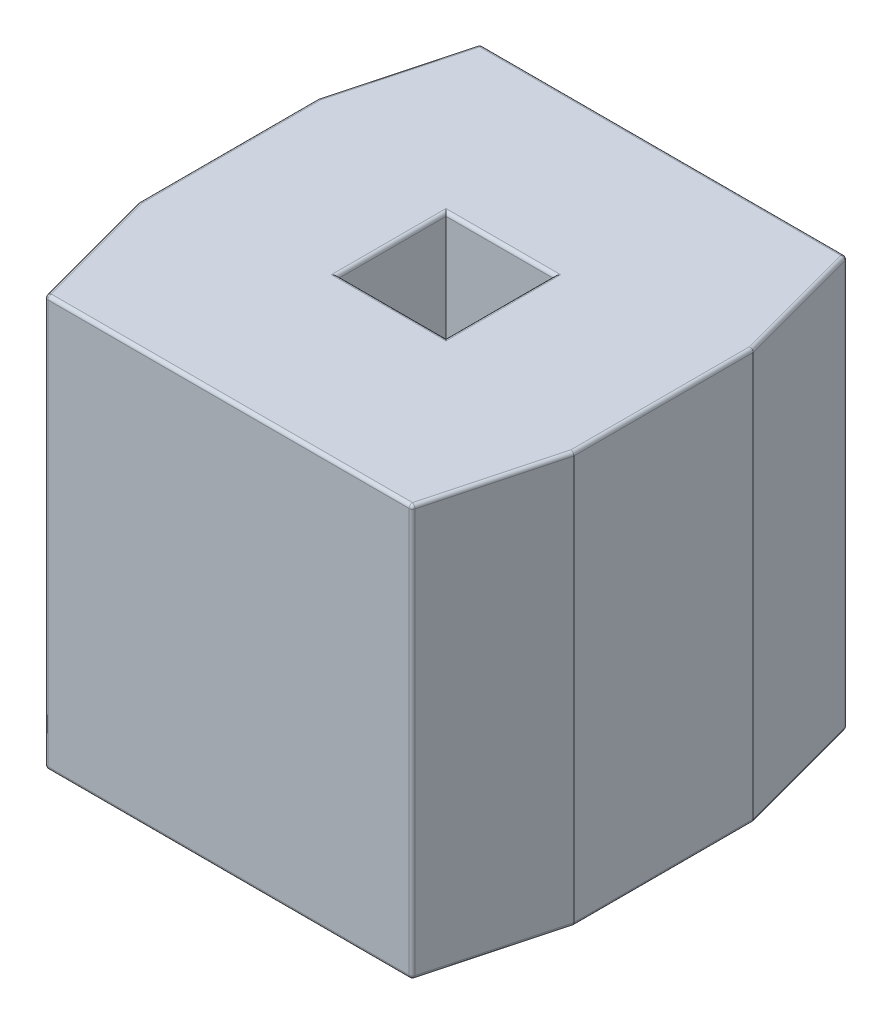
SolidWorks part; units mm, degrees
material "PVC 0.007 Plasticized"
ref_plane "Front Plane" through (0, 0, 0) normal (0, 0, 1) x (1, 0, 0)
ref_plane "Top Plane" through (0, 0, 0) normal (0, 1, 0) x (1, 0, 0)
ref_plane "Right Plane" through (0, 0, 0) normal (1, 0, 0) x (0, 0, -1)
sketch "Sketch1" plane through (0, 0, 0) normal (0, 1, 0) x (1, 0, 0)
  line L1 (-1.27, 1.27) -> (1.27, 1.27)
  line L2 (-1.27, 1.27) -> (-1.27, -1.27)
  line L3 (-1.27, -1.27) -> (1.27, -1.27)
  line L4 (1.27, 1.27) -> (1.27, -1.27)
  line L5 (-1.27, 1.27) -> (1.27, -1.27) construction
  line L6 (-1.27, -1.27) -> (1.27, 1.27) construction
  line L7 (-0.315, 0.315) -> (0.315, 0.315)
  line L8 (-0.315, 0.315) -> (-0.315, -0.315)
  line L9 (-0.315, -0.315) -> (0.315, -0.315)
  line L10 (0.315, 0.315) -> (0.315, -0.315)
  line L11 (-0.315, 0.315) -> (0.315, -0.315) construction
  line L12 (-0.315, -0.315) -> (0.315, 0.315) construction
  point P0 (0, 0)
  point P6 (0, 0)
  dimension "width spacer" = 2.54
  dimension "D2" = 0.63
extrude "Boss-Extrude1" add sketch "Sketch1" along normal blind 2.4
chamfer "Chamfer1" distance 0.2 angle 75 4 edges at (-1.27, 1.2, -1.27) (1.27, 1.2, -1.27) (-1.27, 1.2, 1.27) (1.27, 1.2, 1.27)
fillet "Fillet1" radius 0.02 28 edges at (1.07, 1.2, 1.27) (-1.07, 1.2, 1.27) (1.07, 1.2, -1.27) (-1.07, 1.2, -1.27) (0, 0, 0.315) (-0.315, 0, 0) (0, 0, -0.315) (0.315, 0, 0) (-1.17, 0, 0.8968) (0, 0, 1.27) (1.17, 0, 0.8968) (1.27, 0, 0) (1.17, 0, -0.8968) (0, 0, -1.27) (-1.17, 0, -0.8968) (-1.27, 0, 0) (-0.315, 2.4, 0) (0, 2.4, 0.315) (0.315, 2.4, 0) (0, 2.4, -0.315) (1.17, 2.4, -0.8968) (1.27, 2.4, 0) (1.17, 2.4, 0.8968) (0, 2.4, 1.27) (-1.17, 2.4, 0.8968) (-1.27, 2.4, 0) (-1.17, 2.4, -0.8968) (0, 2.4, -1.27)
equation "\"pin width\"= .63"
equation "\"spacer width\"= 2.54"
equation "\"spacer height\"= 2.4"
equation "\"width spacer@Sketch1\" = \"spacer width\""
equation "\"D1@Boss-Extrude1\"=\"spacer height\""
